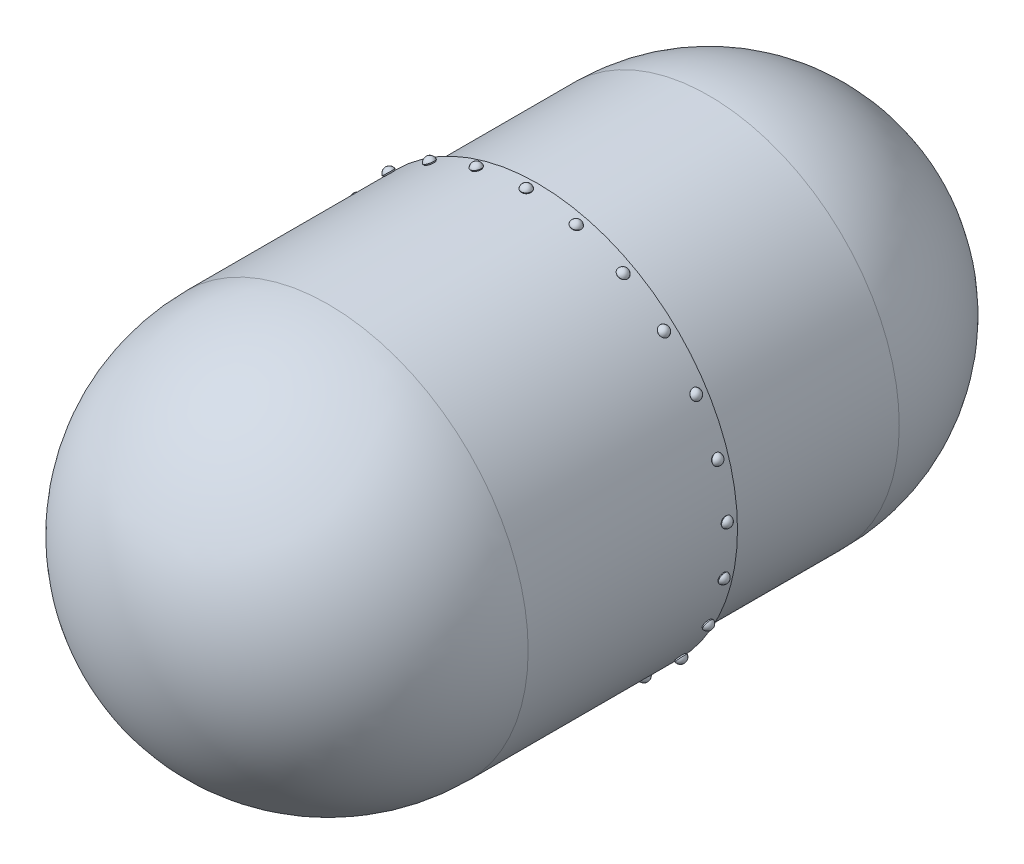
SolidWorks part; units mm, degrees
ref_plane "Front Plane" through (0, 0, 0) normal (0, 0, 1) x (1, 0, 0)
ref_plane "Top Plane" through (0, 0, 0) normal (0, 1, 0) x (1, 0, 0)
ref_plane "Right Plane" through (0, 0, 0) normal (1, 0, 0) x (0, 0, -1)
sketch "Sketch1" plane through (0, 0, 0) normal (0, 0, 1) x (1, 0, 0)
  circle A0 centre (0, 0) radius 1000
  circle A1 centre (0, 0) radius 900
  dimension "D" = 2000
  dimension "t" = 100
extrude "Boss-Extrude1" add sketch "Sketch1" along normal blind 1000
sketch "Sketch2" plane through (0, 0, 1000) normal (0, 0, 1) x (1, 0, 0)
  circle A0 centre (0, 0) radius 1050
  circle A1 centre (0, 0) radius 1000
  dimension "D" = 2000
  dimension "t" = 50
extrude "Boss-Extrude2" add sketch "Sketch2" along normal blind 1000 and the other way blind 100
ref_plane "Plane1" through (0, 0, 900) normal (0, 0, -1) x (-1, 0, 0)
ref_plane "Plane3" through (0, 0, 960) normal (0, 0, -1) x (-1, 0, 0)
sketch "Sketch7" plane through (0, 0, 960) normal (0, 0, -1) x (-1, 0, 0)
  line L0 (0, 0) -> (0, 1764.1602) construction
  line L1 (0, 1050) -> (24, 1050)
  line L2 (24, 1050) -> (27.4641, 1056)
  line L3 (27.4641, 1056) -> (0, 1056)
  line L4 (0, 1056) -> (0, 1050)
  circle A0 centre (0, 0) radius 1050 construction
  point P3 (0, 1050)
  dimension "rvt_rad" = 24
  dimension "rvt_taper_angle" = 120
  dimension "rvt_taper_height" = 6
revolve "Revolve1" add sketch "Sketch7" angle 360 about L0
sketch "Sketch8" plane through (0, 0, 960) normal (0, 0, -1) x (-1, 0, 0)
  line L0 (-24.6928, 1051.2) -> (24.6928, 1051.2) construction
  line L1 (24, 1050) -> (27.4641, 1056) construction
  line L2 (24, 1050) -> (27.4641, 1056) construction
  line L3 (-27.4641, 1056) -> (-24, 1050) construction
  line L4 (0, 1050.2902) -> (0, 1087.9986) construction
  line L5 (27.4641, 1056) -> (-27.4641, 1056) construction
  line L6 (0, 1079.0804) -> (0, 1056)
  line L7 (0, 1056) -> (27.4641, 1056)
  arc A0 (27.4641, 1056) -> (0, 1079.0804) centre (0, 1051.2) ccw
  point P0 (0, 1051.2)
  point P6 (0, 1051.2)
  dimension "arc_center_dist" = 4.8
revolve "Revolve2" add sketch "Sketch8" angle 360 about L6
pattern_circular "CirPattern1" count 25 over 360 about axis through (0, 0, 900) along (0, 0, 1) of bodies 104
sketch "Sketch9" plane through (0, 0, 0) normal (0, 1, 0) x (1, 0, 0)
  line L0 (0, 0) -> (1000, 0)
  line L1 (0, 1000) -> (0, 0)
  arc A0 (1000, 0) -> (0, 1000) centre (0, 0) ccw
revolve "Revolve3" add sketch "Sketch9" angle 360 about L1
sketch "Sketch10" plane through (0, 0, 0) normal (0, 1, 0) x (1, 0, 0)
  line L0 (0, -2000) -> (1050, -2000)
  line L1 (-1050, -2000) -> (1050, -2000) construction
  line L2 (0, -2000) -> (0, -3050)
  arc A0 (1050, -2000) -> (0, -3050) centre (0, -2000) cw
revolve "Revolve4" add sketch "Sketch10" angle 360 about L2
ref_plane "Plane5" through (0, 0, 1090) normal (0, 0, 1) x (1, 0, 0)
ref_plane "Plane7" through (0, 0, 900) normal (0, 0, -1) x (-1, 0, 0)
sketch "Sketch11" plane through (0, 0, 900) normal (0, 0, -1) x (-1, 0, 0)
  line L0 (0, 0) -> (0, 1888.8947) construction
  line L1 (0, 0) -> (-244.0759, 1888.8947) construction
  circle A0 centre (0, 0) radius 1050 construction
  point P3 (0, 1050)
  point P5 (-134.5584, 1041.3424)
  dimension "dist_for_diagonal" = 134.9294
